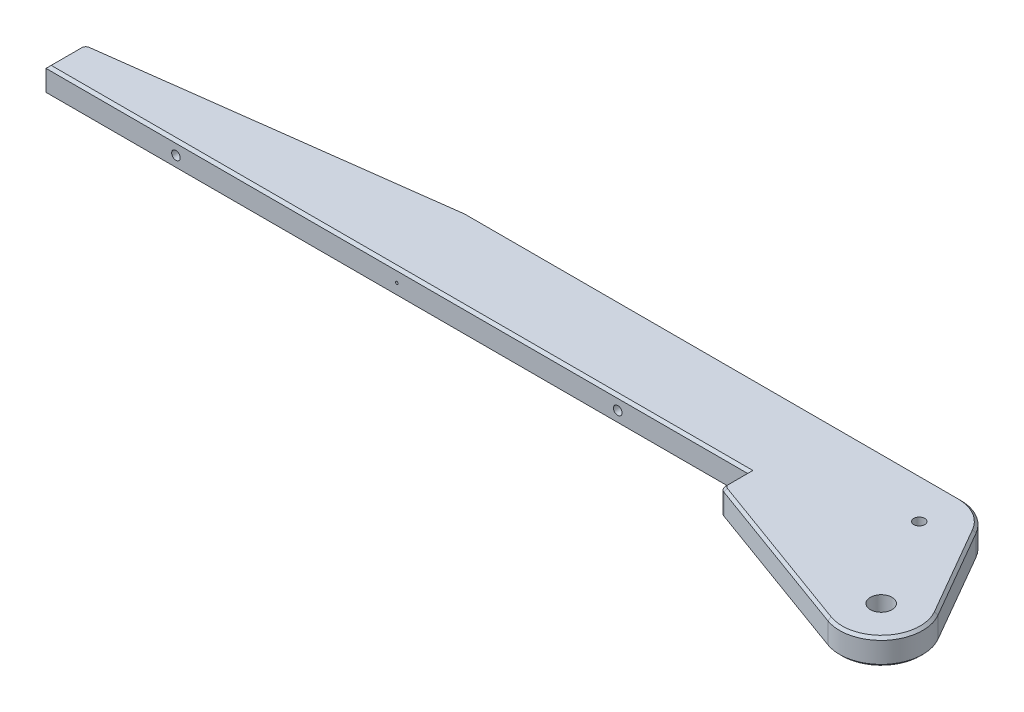
SolidWorks part; units mm, degrees
ref_plane "Front Plane" through (0, 0, 0) normal (0, 0, 1) x (1, 0, 0)
ref_plane "Top Plane" through (0, 0, 0) normal (0, 1, 0) x (1, 0, 0)
ref_plane "Right Plane" through (0, 0, 0) normal (1, 0, 0) x (0, 0, -1)
sketch "Sketch2" plane through (0, 0, 0) normal (0, 1, 0) x (1, 0, 0)
  line L0 (-210, 50.641) -> (-20, 50.641)
  line L1 (-6.1436, 42.641) -> (13.8564, 8)
  line L2 (-340, 33.641) -> (-340, 18.641)
  line L3 (-340, 18.641) -> (-70, 18.641)
  line L5 (-340, 33.641) -> (-210, 50.641)
  line L6 (-70, 18.641) -> (-70, 8.4511)
  line L7 (-5.4723, -15.0351) -> (-70, 8.4511)
  circle A1 centre (0, 0) radius 40 construction
  arc A2 (-6.1436, 42.641) -> (-20, 50.641) centre (-20, 34.641) ccw
  arc A3 (-5.4723, -15.0351) -> (13.8564, 8) centre (0, 0) ccw
  point P1 (-20, 34.641)
  dimension "D1" = 20
  dimension "D3" = 40
  dimension "D4" = 80
  dimension "D10" = 32
  dimension "D2" = 190
  dimension "D5" = 130
  dimension "D6" = 15
  dimension "D7" = 32
  dimension "D9" = 270
extrude "Boss-Extrude1" add sketch "Sketch2" along normal mid plane 10
hole_wizard "M5x0.8 Tapped Hole1" positions "Sketch3" profile "Sketch4" tap size "M5x0.8" standard "ANSI Metric" end condition through all
sketch "Sketch3" plane through (0, 5, 0) normal (0, 1, 0) x (1, 0, 0)
  point P0 (-20, 34.641)
  point P2 (0, 0)
sketch "Sketch4" plane through (-20, 5, -34.641) normal (1, 0, 0) x (0, 0, 1)
  line L0 (0, 0) -> (0, 10)
  line L1 (0, 10) -> (2.1, 10)
  line L2 (2.1, 10) -> (2.1, 0)
  line L5 (2.1, 0) -> (0, 0)
  line L11 (0, -6.35) -> (0, 107.95) construction
  dimension "Thru Tap Drill Dia." = 4.2
  dimension "Thru Tap Drill Depth" = 10
cosmetic thread "Hole Thread1" parameters "D2"=5
cosmetic thread "Hole Thread2" parameters "D2"=5
sketch "Sketch5" plane through (0, 5, 0) normal (0, 1, 0) x (1, 0, 0)
  circle A0 centre (0, 0) radius 4.15
  dimension "D1" = 8.3
extrude "Cut-Extrude1" cut sketch "Sketch5" against normal blind 6
hole_wizard "M4x0.7 Tapped Hole1" positions "Sketch12" profile "Sketch13" tap size "M4x0.7" standard "ANSI Metric"
sketch "Sketch12" plane through (0, 0, -18.641) normal (0, 0, 1) x (1, 0, 0)
  line L0 (49.8526, 0) -> (-49.8526, 0) construction
  line L1 (-340, 5) -> (-340, -5) construction
  line L2 (-70, 5) -> (-70, -5) construction
  point P0 (-290, 0)
  point P2 (-120, 0)
  dimension "D1" = 50
  dimension "D2" = 50
sketch "Sketch13" plane through (-290, 0, -18.641) normal (1, 0, 0) x (0, -1, 0)
  line L0 (0, 0) -> (0, 15.9914)
  line L1 (0, 15.9914) -> (1.65, 15)
  line L2 (1.65, 15) -> (1.65, 0)
  line L5 (1.65, 0) -> (0, 0)
  line L10 (0, 15.9914) -> (-1.65, 15) construction
  line L11 (0, -6.35) -> (0, 107.95) construction
  dimension "Tap Drill Dia." = 3.3
  dimension "Tap Drill Depth" = 15
  dimension "Drill Angle" = 118
cosmetic thread "Hole Thread3" parameters "D1"=14.3, "D2"=4
cosmetic thread "Hole Thread4" parameters "D1"=14.3, "D2"=4
fillet "Fillet1" radius 2.5 3 edges at (-70, 0, -8.4511) (-210, 0, -50.641) (-340, 0, -33.641)
chamfer "Chamfer1" distance 1 angle 45 24 edges at (-70, -5, -14.4213) (-69.5479, -5, -8.7676) (-36.9137, -5, 3.5914) (12.2567, -5, 10.2846) (3.8564, -5, -25.3205) (-12, -5, -48.4974) (-114.9186, -5, -50.641) (-209.9997, -5, -50.6357) (-273.9928, -5, -42.2727) (-339.3789, -5, -33.0958) (-340, -5, -25.0438) (-205, -5, -18.641) (-209.9997, 5, -50.6357) (-114.9186, 5, -50.641) (-12, 5, -48.4974) (3.8564, 5, -25.3205) (12.2567, 5, 10.2846) (-36.9137, 5, 3.5914) (-69.5479, 5, -8.7676) (-70, 5, -14.4213) (-205, 5, -18.641) (-340, 5, -25.0438) (-339.3789, 5, -33.0958) (-273.9928, 5, -42.2727)
hole_wizard "Ø1.0mm Dowel Hole1" positions "Sketch14" profile "Sketch15" hole size "Ø1.0" standard "ANSI Metric"
sketch "Sketch14" plane through (0, 0, -18.641) normal (0, 0, 1) x (1, 0, 0)
  line L0 (36.6526, 0) -> (-36.6526, 0) construction
  circle A0 centre (-290, 0) radius 1.65 construction
  point P0 (-205, 0)
  dimension "D1" = 85
sketch "Sketch15" plane through (-205, 0, -18.641) normal (1, 0, 0) x (0, -1, 0)
  line L0 (0, 0) -> (0, 5.3004)
  line L1 (0, 5.3004) -> (0.5, 5)
  line L2 (0.5, 5) -> (0.5, 0)
  line L5 (0.5, 0) -> (0, 0)
  line L10 (0, 5.3004) -> (-0.5, 5) construction
  line L11 (0, -6.35) -> (0, 107.95) construction
  dimension "Hole Dia." = 1
  dimension "Hole Depth" = 5
  dimension "Drill Angle" = 118
